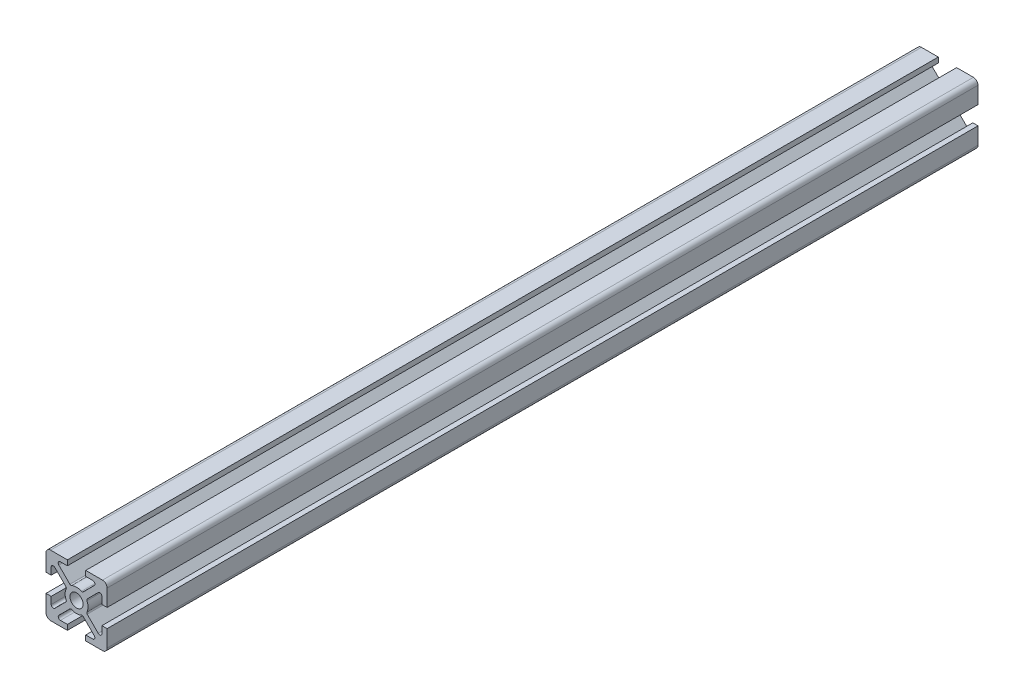
SolidWorks part; units mm, degrees
material "6063-T5"
ref_plane "Face" through (0, 0, 0) normal (0, 0, 1) x (1, 0, 0)
ref_plane "Dessus" through (0, 0, 0) normal (0, 1, 0) x (1, 0, 0)
ref_plane "Droite" through (0, 0, 0) normal (1, 0, 0) x (0, 0, -1)
sketch "Esquisse1" plane through (0, 0, 0) normal (0, 0, 1) x (1, 0, 0)
  line L0 (-3, 10) -> (-8.5, 10)
  line L2 (-3, -10) -> (-3, -8.3)
  line L3 (-3, -8.3) -> (-5.2994, -8.3)
  line L4 (-5.7944, -7.105) -> (-2.1755, -3.4861)
  line L6 (2.1755, -3.4861) -> (5.7944, -7.105)
  line L7 (5.2994, -8.3) -> (3, -8.3)
  line L8 (3, -8.3) -> (3, -10)
  line L11 (3, -10) -> (8.5, -10)
  line L12 (10, -8.5) -> (10, -3)
  line L15 (10, -3) -> (8.3, -3)
  line L16 (8.3, -3) -> (8.3, -5.2994)
  line L17 (7.105, -5.7944) -> (3.4861, -2.1755)
  line L20 (3.4861, 2.1755) -> (7.105, 5.7944)
  line L21 (8.3, 5.2994) -> (8.3, 3)
  line L22 (8.3, 3) -> (10, 3)
  line L25 (10, 3) -> (10, 8.5)
  line L26 (8.5, 10) -> (3.5, 10)
  line L29 (3, 10) -> (3, 8.3)
  line L30 (3, 8.3) -> (5.2994, 8.3)
  line L31 (5.7944, 7.105) -> (2.1755, 3.4861)
  line L34 (-2.1755, 3.4861) -> (-5.7944, 7.105)
  line L35 (-5.2994, 8.3) -> (-3, 8.3)
  line L36 (-3, 8.3) -> (-3, 10)
  line L39 (3.5, 10) -> (3, 10)
  line L40 (-10, 8.5) -> (-10, 3)
  line L43 (-10, 3) -> (-8.3, 3)
  line L44 (-8.3, 3) -> (-8.3, 5.2994)
  line L45 (-7.105, 5.7944) -> (-3.4861, 2.1755)
  line L48 (-3.4861, -2.1755) -> (-7.105, -5.7944)
  line L49 (-8.3, -5.2994) -> (-8.3, -3)
  line L50 (-8.3, -3) -> (-10, -3)
  line L53 (-10, -3) -> (-10, -8.5)
  line L54 (-8.5, -10) -> (-3, -10)
  line L55 (13.1941, 0) -> (-16.3684, 0) construction
  line L56 (0, 3.75) -> (0, -15.1011) construction
  line L58 (5.7944, 5.7944) -> (-5.2994, -5.2994) construction
  line L59 (5.7944, -5.7944) -> (-5.4107, 5.4107) construction
  circle A0 centre (0, 0) radius 2.15
  arc A1 (-5.2994, -8.3) -> (-5.7944, -7.105) centre (-5.2994, -7.6) cw
  arc A2 (-2.1755, -3.4861) -> (-1.6076, -3.388) centre (-1.8219, -3.8397) cw
  arc A3 (-1.6076, -3.388) -> (1.6076, -3.388) centre (0, 0) ccw
  arc A5 (1.6076, -3.388) -> (2.1755, -3.4861) centre (1.8219, -3.8397) cw
  arc A6 (5.7944, -7.105) -> (5.2994, -8.3) centre (5.2994, -7.6) cw
  arc A7 (8.5, -10) -> (10, -8.5) centre (8.5, -8.5) ccw
  arc A8 (8.3, -5.2994) -> (7.105, -5.7944) centre (7.6, -5.2994) cw
  arc A9 (3.4861, -2.1755) -> (3.388, -1.6076) centre (3.8397, -1.8219) cw
  arc A10 (3.388, -1.6076) -> (3.75, 0) centre (0, 0) ccw
  arc A11 (3.75, 0) -> (3.388, 1.6076) centre (0, 0) ccw
  arc A12 (3.388, 1.6076) -> (3.4861, 2.1755) centre (3.8397, 1.8219) cw
  arc A13 (7.105, 5.7944) -> (8.3, 5.2994) centre (7.6, 5.2994) cw
  arc A14 (10, 8.5) -> (8.5, 10) centre (8.5, 8.5) ccw
  arc A15 (5.2994, 8.3) -> (5.7944, 7.105) centre (5.2994, 7.6) cw
  arc A16 (2.1755, 3.4861) -> (1.6076, 3.388) centre (1.8219, 3.8397) cw
  arc A17 (1.6076, 3.388) -> (-1.6076, 3.388) centre (0, 0) ccw
  arc A19 (-1.6076, 3.388) -> (-2.1755, 3.4861) centre (-1.8219, 3.8397) cw
  arc A20 (-5.7944, 7.105) -> (-5.2994, 8.3) centre (-5.2994, 7.6) cw
  arc A21 (-8.5, 10) -> (-10, 8.5) centre (-8.5, 8.5) ccw
  arc A22 (-8.3, 5.2994) -> (-7.105, 5.7944) centre (-7.6, 5.2994) cw
  arc A23 (-3.4861, 2.1755) -> (-3.388, 1.6076) centre (-3.8397, 1.8219) cw
  arc A24 (-3.388, 1.6076) -> (-3.388, -1.6076) centre (0, 0) ccw
  arc A26 (-3.388, -1.6076) -> (-3.4861, -2.1755) centre (-3.8397, -1.8219) cw
  arc A27 (-7.105, -5.7944) -> (-8.3, -5.2994) centre (-7.6, -5.2994) cw
  arc A28 (-10, -8.5) -> (-8.5, -10) centre (-8.5, -8.5) ccw
  dimension "D3" = 4.3
  dimension "D4" = 1.5
  dimension "D15" = 0.7
  dimension "D19" = 3.75
  dimension "D20" = 0.5
  dimension "D1" = 20
  dimension "D2" = 20
  dimension "D10" = 10
  dimension "D11" = 10
  dimension "D12" = 3
  dimension "D13" = 3
  dimension "D16" = 1.7
  dimension "D17" = 5.2994
  dimension "D18" = 45
  dimension "D22" = 45
  dimension "D23" = 6
  dimension "D24" = 45
  dimension "D25" = 5.2994
  dimension "D26" = 45
extrude "Boss.-Extru.1" add sketch "Esquisse1" along normal blind 285
